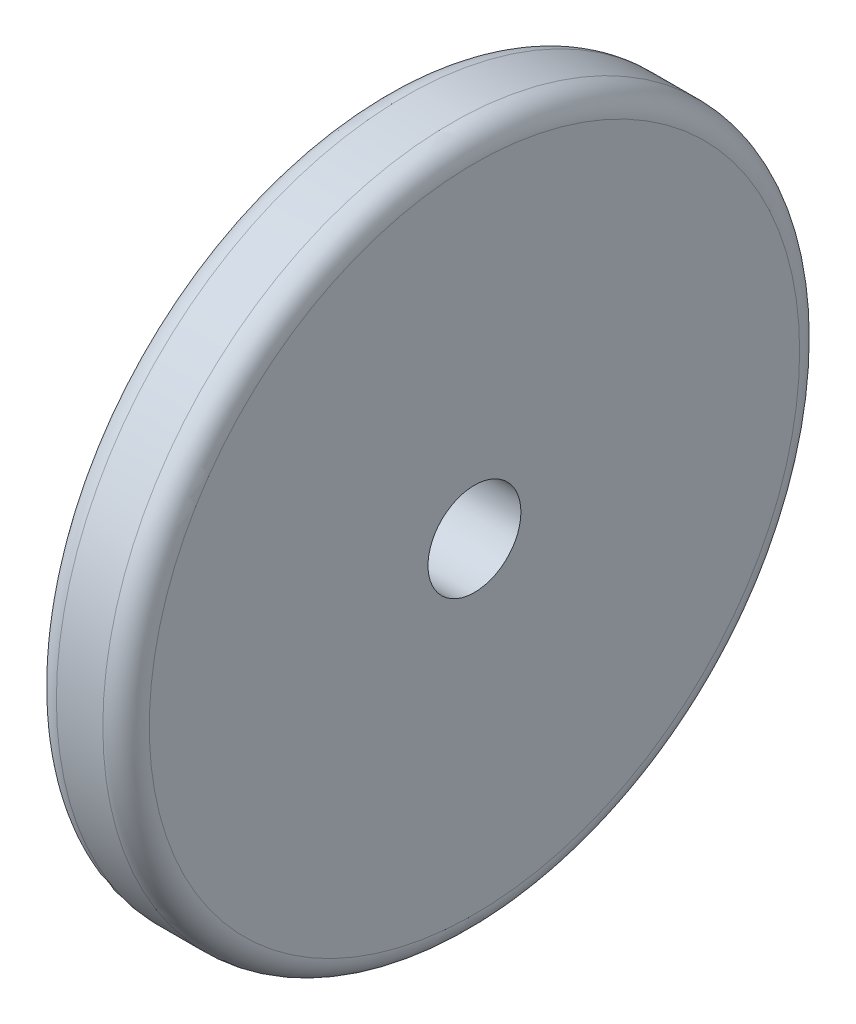
SolidWorks part; units mm, degrees
material "PMMA"
ref_plane "Front Plane" through (0, 0, 0) normal (0, 0, 1) x (1, 0, 0)
ref_plane "Top Plane" through (0, 0, 0) normal (0, 1, 0) x (1, 0, 0)
ref_plane "Right Plane" through (0, 0, 0) normal (1, 0, 0) x (0, 0, -1)
sketch "Schizzo1" plane through (0, 0, 0) normal (1, 0, 0) x (0, 0, -1)
  circle A0 centre (0, 0) radius 30
  dimension "D1" = 60
extrude "Estrusione-Estrusione1" add sketch "Schizzo1" along normal blind 8
sketch "Schizzo3" plane through (8, 0, 0) normal (1, 0, 0) x (0, 0, -1)
  circle A0 centre (0, 0) radius 4
  dimension "D1" = 8
extrude "Taglio-Estrusione1" cut sketch "Schizzo3" against normal through all
fillet "Raccordo1" radius 2 2 edges at (8, 0, -30) (0, 0, -30)
equation "\"Thickness8\"=8"
equation "\"D1@Estrusione-Estrusione1\"=\"Thickness8\""
